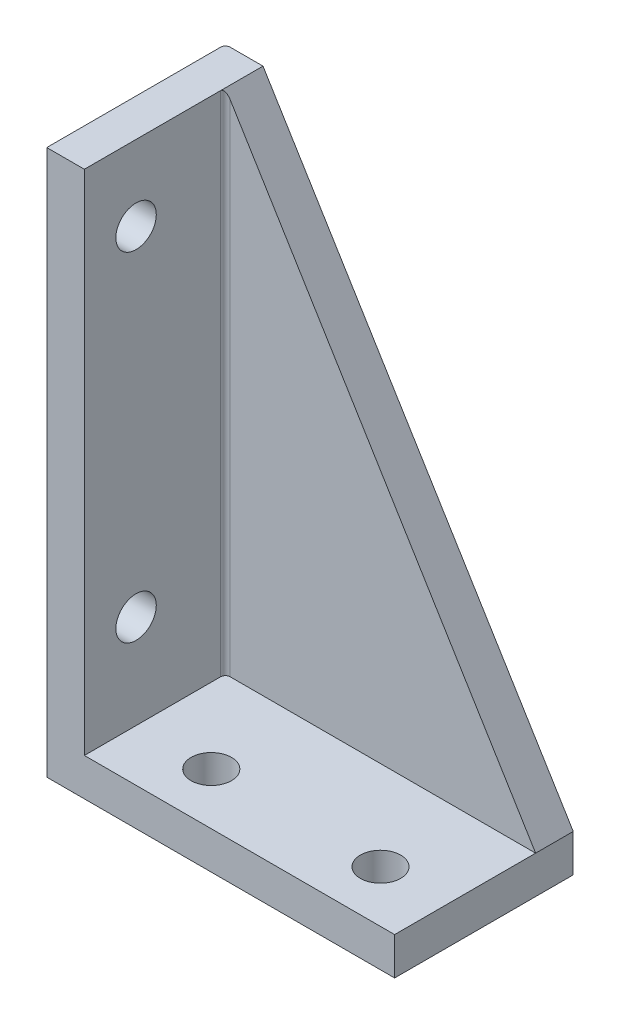
SolidWorks part; units mm, degrees
material "80% - PLA"
ref_plane "Front Plane" through (0, 0, 0) normal (0, 0, 1) x (1, 0, 0)
ref_plane "Top Plane" through (0, 0, 0) normal (0, 1, 0) x (1, 0, 0)
ref_plane "Right Plane" through (0, 0, 0) normal (1, 0, 0) x (0, 0, -1)
sketch "Sketch1" plane through (0, 0, 0) normal (0, 0, 1) x (1, 0, 0)
  line L1 (0, 0) -> (37, 0)
  line L2 (0, 0) -> (0, 58)
  line L3 (0, 58) -> (37, 58)
  line L4 (37, 0) -> (37, 58)
  dimension "D1" = 58
  dimension "D2" = 37
extrude "Boss-Extrude1" add sketch "Sketch1" along normal blind 30
sketch "Sketch2" plane through (0, 58, 0) normal (0, 1, 0) x (1, 0, 0)
  line L0 (37, -15) -> (0, -15)
  line L1 (37, -30) -> (37, 0) construction
  line L2 (0, -30) -> (0, 0) construction
  line L3 (37, -13) -> (0, -13)
  line L4 (37, -17) -> (0, -17)
  line L5 (37, 0) -> (0, 0) construction
  line L6 (37, 0) -> (4, 0)
  line L7 (37, 0) -> (37, -13)
  line L8 (37, -13) -> (4, -13)
  line L9 (4, 0) -> (4, -13)
  line L11 (37, -30) -> (4, -30)
  line L12 (37, -30) -> (37, -17)
  line L13 (37, -17) -> (4, -17)
  line L14 (4, -30) -> (4, -17)
  line M3 (37, 0) -> (0, 0)
  line M5 (0, -30) -> (37, -30)
  line M6 (37, -30) -> (37, 0)
  dimension "D3" = 33
  dimension "D4" = 33
  dimension "D1" = 2
  dimension "D2" = 2
extrude "Cut-Extrude1" cut sketch "Sketch2" against normal blind 54 contours L9 L3 M3 M6 | L14 L4 M5 M6
sketch "Sketch3" plane through (0, 0, 13) normal (0, 0, 1) x (1, 0, 0)
  line L0 (4, 58) -> (37, 4)
  line L1 (37, 4) -> (37, 58)
  line L2 (37, 58) -> (4, 58)
  dimension "D1" = 33
extrude "Cut-Extrude2" cut sketch "Sketch3" along normal blind 46
hole_wizard "M4 Clearance Hole1" positions "Sketch5" profile "Sketch4" hole size "M4" standard "ISO" end condition through all
sketch "Sketch5" plane through (4, 0, 0) normal (1, 0, 0) x (0, 0, -1)
  line L0 (0, 58) -> (-13, 58) construction
  line L1 (-13, 4) -> (0, 4) construction
  line L7 (-30, 4) -> (-30, 58) construction
  point P3 (-26.5, 14)
  point P5 (-26.5, 50)
  dimension "D1" = 8
  dimension "D2" = 10
  dimension "D3" = 3.5
  dimension "D4" = 3.5
sketch "Sketch4" plane through (4, 14, 26.5) normal (0, 1, 0) x (0, 0, -1)
  line L0 (0, 0) -> (0, 4)
  line L1 (0, 4) -> (2.15, 4)
  line L2 (2.15, 4) -> (2.15, 0)
  line L5 (2.15, 0) -> (0, 0)
  line L11 (0, -6.35) -> (0, 107.95) construction
  dimension "Thru Hole Dia." = 4.3
  dimension "Thru Hole Depth" = 4
hole_wizard "M4 Clearance Hole2" positions "Sketch7" profile "Sketch6" hole size "M4" standard "ISO" end condition through all
sketch "Sketch7" plane through (0, 4, 0) normal (0, 1, 0) x (1, 0, 0)
  line L1 (4, 0) -> (4, -13) construction
  line L2 (37, -13) -> (37, 0) construction
  line L3 (4, -30) -> (37, -30) construction
  point P0 (12, -26.5)
  point P2 (30, -26.5)
  dimension "D1" = 3.5
  dimension "D2" = 8
  dimension "D3" = 7
  dimension "D4" = 3.5
sketch "Sketch6" plane through (12, 4, 26.5) normal (1, 0, 0) x (0, 0, 1)
  line L0 (0, 0) -> (0, 4)
  line L1 (0, 4) -> (2.15, 4)
  line L2 (2.15, 4) -> (2.15, 0)
  line L5 (2.15, 0) -> (0, 0)
  line L11 (0, -6.35) -> (0, 107.95) construction
  dimension "Thru Hole Dia." = 4.3
  dimension "Thru Hole Depth" = 4
sketch "Sketch8" plane through (0, 4, 0) normal (0, 1, 0) x (1, 0, 0)
  line L1 (37, -13) -> (0, -13)
  line L2 (37, -13) -> (37, 0)
  line L3 (37, 0) -> (0, 0)
  line L4 (0, -13) -> (0, 0)
extrude "Cut-Extrude3" cut sketch "Sketch8" against normal blind 10 and the other way through all
fillet "Fillet1" radius 0.5 2 edges at (4, 31, 17) (0, 29, 13)
sketch "Sketch9" plane through (0, 0, 30) normal (0, 0, 1) x (1, 0, 0)
  line L0 (0, 58) -> (4, 58)
  line L1 (4, 4) -> (4, 58) construction
  line L2 (4, 58) -> (0, 58) construction
  line L3 (4, 58) -> (4, 4)
  line L4 (4, 4) -> (37, 4)
  line L5 (37, 4) -> (37, 0)
  line L6 (37, 0) -> (0, 0)
  line L7 (0, 0) -> (0, 58)
extrude "Boss-Extrude2" add sketch "Sketch9" along normal blind 2
